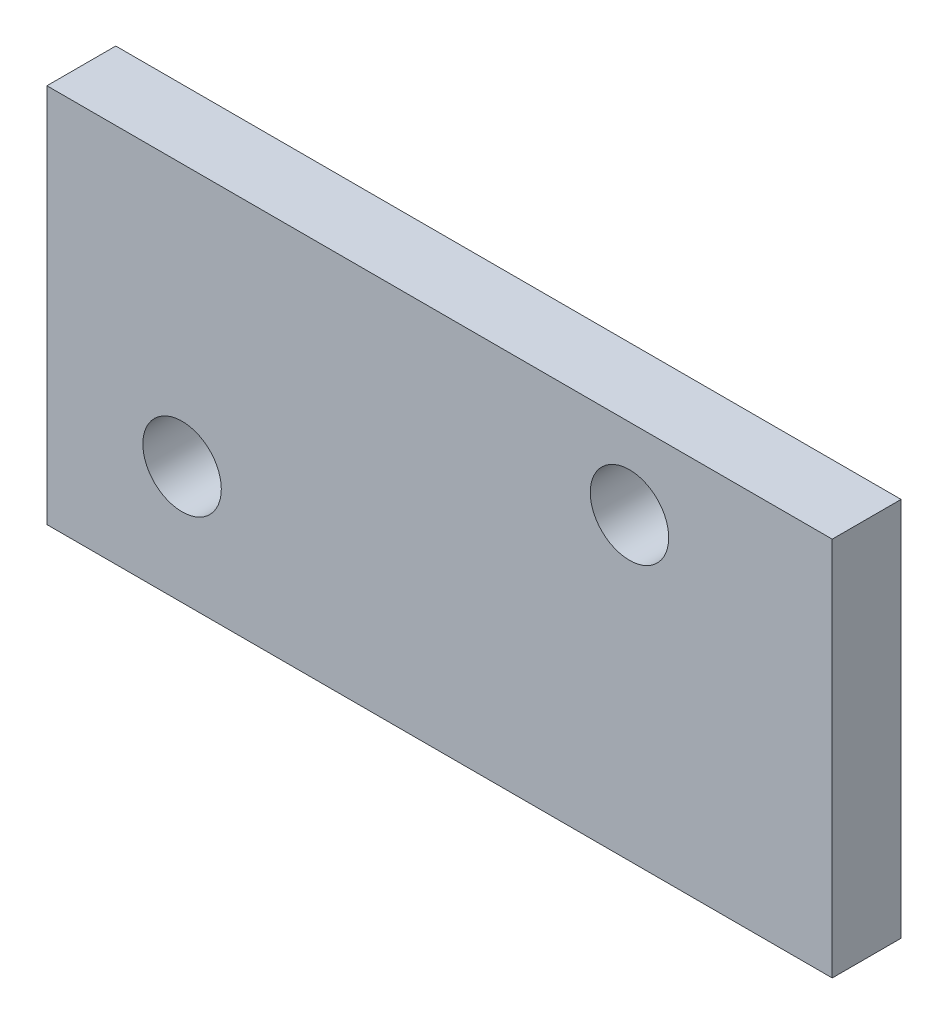
SolidWorks part; units mm, degrees
ref_plane "Front Plane" through (0, 0, 0) normal (0, 0, 1) x (1, 0, 0)
ref_plane "Top Plane" through (0, 0, 0) normal (0, 1, 0) x (1, 0, 0)
ref_plane "Right Plane" through (0, 0, 0) normal (1, 0, 0) x (0, 0, -1)
sketch "Sketch1" plane through (0, 0, 0) normal (0, 0, 1) x (1, 0, 0)
  line L1 (-205.2612, 147.3638) -> (-176.2817, 147.3638)
  line L2 (-205.2612, 147.3638) -> (-205.2612, 161.389)
  line L3 (-205.2612, 161.389) -> (-176.2817, 161.389)
  line L4 (-176.2817, 147.3638) -> (-176.2817, 161.389)
  circle A2 centre (-183.7642, 158.4192) radius 1.4478
  circle A3 centre (-200.2742, 151.7136) radius 1.4478
  point P5 (-176.2817, 147.3638)
  point P7 (-205.2612, 161.389)
extrude "Boss-Extrude1" add sketch "Sketch1" along normal blind 2.54
